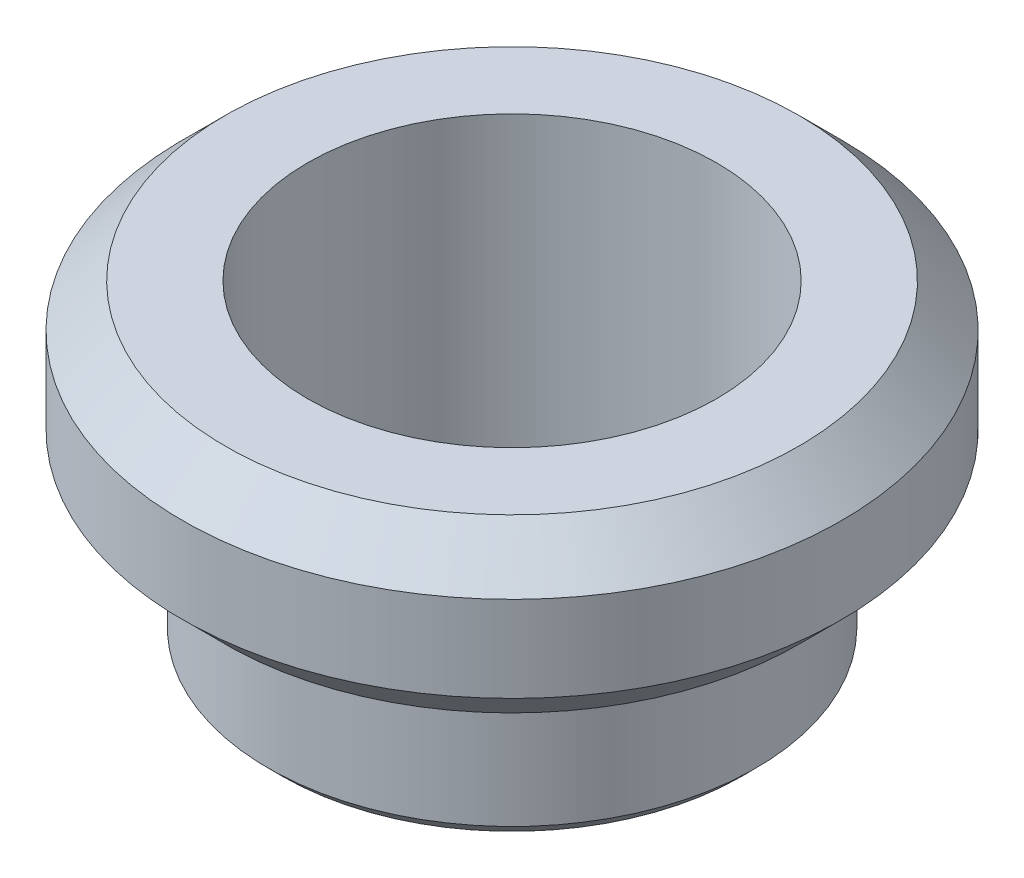
SolidWorks part; units mm, degrees
ref_plane "Front Plane" through (0, 0, 0) normal (0, 0, 1) x (1, 0, 0)
ref_plane "Top Plane" through (0, 0, 0) normal (0, 1, 0) x (1, 0, 0)
ref_plane "Right Plane" through (0, 0, 0) normal (1, 0, 0) x (0, 0, -1)
sketch "Sketch2" plane through (0, 0, 0) normal (1, 0, 0) x (0, 0, -1)
  line L0 (0, 0) -> (14.3, 0) construction
  line L3 (14.3, 0) -> (17.05, 0)
  line L4 (14.3, 0) -> (14.3, -10)
  line L5 (14.3, -10) -> (17.05, -10)
  line L6 (17.05, 0) -> (17.05, -10)
  line L7 (14.3, 0) -> (23.05, 0)
  line L8 (14.3, 0) -> (14.3, 12)
  line L9 (14.3, 12) -> (23.05, 12)
  line L10 (23.05, 0) -> (23.05, 12)
  point P10 (0, 0)
  dimension "D1" = 17.05
  dimension "D2" = 14.3
  dimension "D3" = 6
  dimension "D4" = 10
  dimension "D5" = 12
ref_axis "Axis1" through (0, -11.25, 0) along (0, 1, 0)
revolve "Revolve1" add sketch "Sketch2" angle 360 about axis through (0, -11.25, 0) along (0, 1, 0)
chamfer "Chamfer1" distance 3 angle 45 2 edges at (0, 12, -23.05) (0, 0, -23.05)
chamfer "Chamfer2" distance 1 angle 45 1 edges at (0, -10, -17.05)
